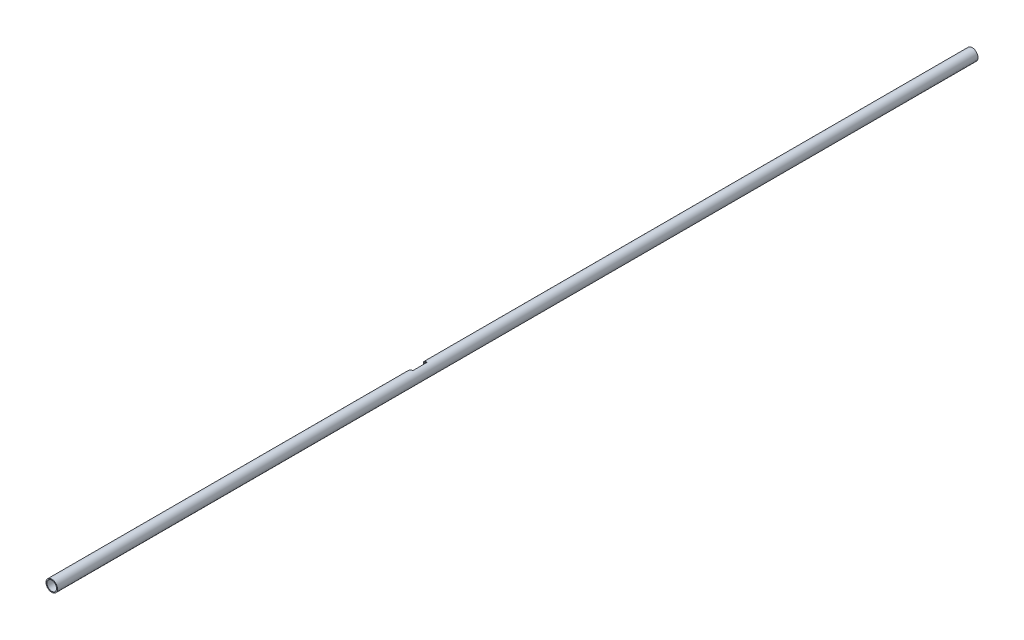
SolidWorks part; units mm, degrees
material "PVC Rigid"
ref_plane "Front Plane" through (0, 0, 0) normal (0, 0, 1) x (1, 0, 0)
ref_plane "Top Plane" through (0, 0, 0) normal (0, 1, 0) x (1, 0, 0)
ref_plane "Right Plane" through (0, 0, 0) normal (1, 0, 0) x (0, 0, -1)
sketch "Sketch1" plane through (0, 0, 0) normal (0, 0, 1) x (1, 0, 0)
  circle A0 centre (0, 0) radius 19.05
  circle A2 centre (0, 0) radius 15.875
  dimension "D1" = 38.1
  dimension "D2" = 31.75
extrude "Boss-Extrude1" add sketch "Sketch1" along normal blind 3048
sketch "Sketch2" plane through (0, 0, 0) normal (1, 0, 0) x (0, 0, -1)
  circle A0 centre (-1828.8, 0) radius 30.226
  dimension "D1" = 60.452
  dimension "D2" = 1219.2
extrude "Cut-Extrude1" cut sketch "Sketch2" against normal through all
